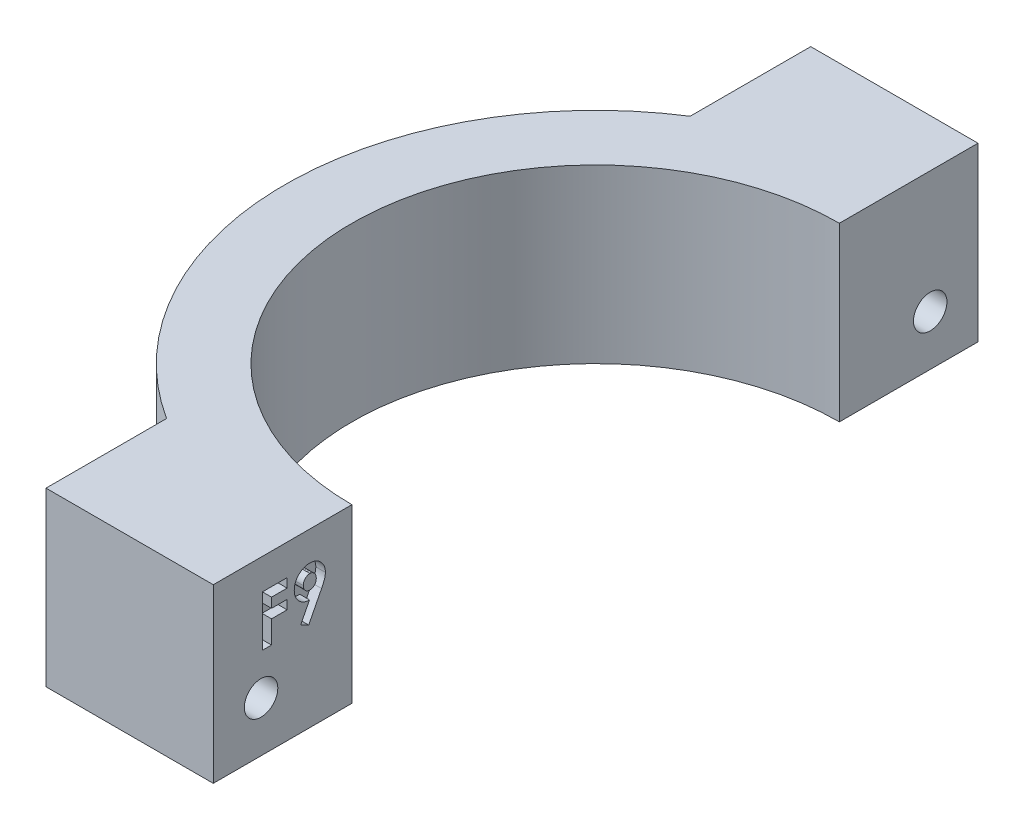
SolidWorks part; units mm, degrees
ref_plane "Front Plane" through (0, 0, 0) normal (0, 0, 1) x (1, 0, 0)
ref_plane "Top Plane" through (0, 0, 0) normal (0, 1, 0) x (1, 0, 0)
ref_plane "Right Plane" through (0, 0, 0) normal (1, 0, 0) x (0, 0, -1)
sketch "Sketch1" plane through (0, 0, 0) normal (0, 1, 0) x (1, 0, 0)
  line L0 (-46.9983, 32.5286) -> (-46.9983, -47.4714)
  line L1 (-46.9983, -47.4714) -> (-11.9983, -47.4714)
  line L2 (-11.9983, -47.4714) -> (-11.9983, -32.9714)
  line L3 (-46.9983, 32.5286) -> (-11.9983, 32.5286)
  line L4 (-11.9983, 32.5286) -> (-11.9983, 18.0286)
  line L5 (-29.4983, 32.5286) -> (-29.4983, 19.9147)
  line L6 (-29.4983, -47.4714) -> (-29.4983, -34.8576)
  arc A0 (-11.9983, 18.0286) -> (-11.9983, -32.9714) centre (-11.9983, -7.4714) ccw
  arc A1 (-11.9983, 25.0286) -> (-11.9983, -39.9714) centre (-11.9983, -7.4714) ccw
  dimension "D1" = 80
  dimension "D2" = 35
  dimension "D3" = 35
  dimension "D4" = 51
  dimension "D5" = 14.5
  dimension "D6" = 14.5
  dimension "D7" = 7
extrude "Boss-Extrude1" add sketch "Sketch1" along normal blind 18 contours A1 L4 L3 L5 | L4 A1 L2 A0 | A1 L6 L1 L2
sketch "Sketch2" plane through (-11.9983, 0, 0) normal (1, 0, 0) x (0, 0, -1)
  line L0 (-47.4714, 18) -> (-32.9714, 18) construction
  line L3 (32.5286, 18) -> (18.0286, 18) construction
  circle A0 centre (-42.4714, 5.25) radius 1.75
  circle A1 centre (27.5286, 5.25) radius 1.75
  dimension "D3" = 3.5
  dimension "D4" = 3.5
  dimension "D1" = 12.75
  dimension "D2" = 12.75
extrude "Cut-Extrude1" cut sketch "Sketch2" against normal through all
sketch "Sketch3" plane through (-11.9983, 0, 0) normal (1, 0, 0) x (0, 0, -1)
  text T0 "<b>F9</b>" font "Century Gothic" height in points 20
extrude "Cut-Extrude2" cut sketch "Sketch3" against normal blind 1
sketch "Sketch4" plane through (-29.4983, 0, 0) normal (-1, 0, 0) x (0, 0, 1)
  line L1 (-25.3918, 2.9011) -> (-24.4259, 5.926)
  line L2 (-24.4259, 5.926) -> (-26.5627, 8.275)
  line L3 (-26.5627, 8.275) -> (-29.6653, 7.5989)
  line L4 (-29.6653, 7.5989) -> (-30.6312, 4.574)
  line L5 (-30.6312, 4.574) -> (-28.4944, 2.225)
  line L6 (-28.4944, 2.225) -> (-25.3918, 2.9011)
  line L7 (44.7168, 3.0046) -> (45.5387, 6.0719)
  line L8 (45.5387, 6.0719) -> (43.2933, 8.3172)
  line L9 (43.2933, 8.3172) -> (40.2261, 7.4954)
  line L10 (40.2261, 7.4954) -> (39.4042, 4.4281)
  line L11 (39.4042, 4.4281) -> (41.6496, 2.1828)
  line L12 (41.6496, 2.1828) -> (44.7168, 3.0046)
  circle A0 centre (-27.5286, 5.25) radius 2.75 construction
  circle A1 centre (42.4714, 5.25) radius 2.75 construction
  dimension "D1" = 5.5
extrude "Cut-Extrude3" cut sketch "Sketch4" against normal blind 5
